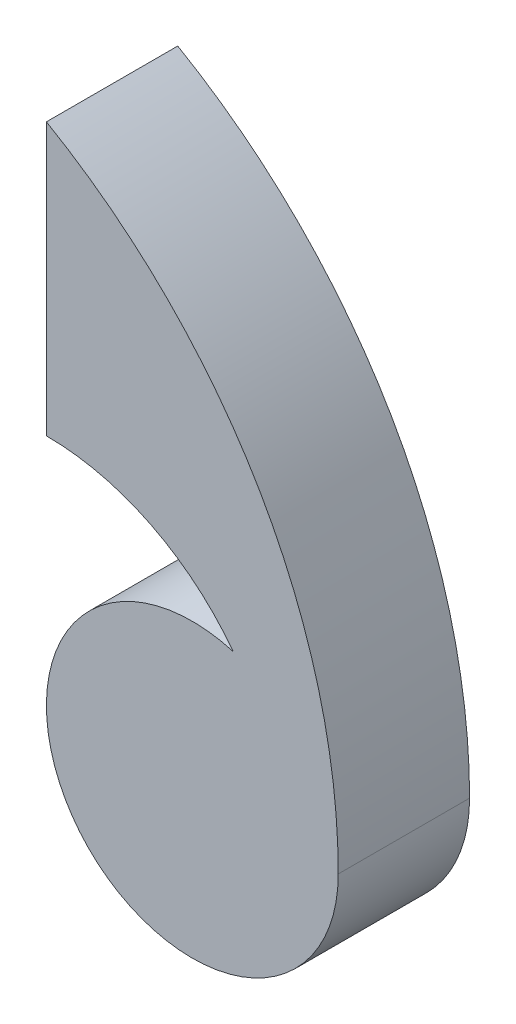
SolidWorks part; units mm, degrees
ref_plane "前视基准面" through (0, 0, 0) normal (0, 0, 1) x (1, 0, 0)
ref_plane "上视基准面" through (0, 0, 0) normal (0, 1, 0) x (1, 0, 0)
ref_plane "右视基准面" through (0, 0, 0) normal (1, 0, 0) x (0, 0, -1)
sketch "草图1" plane through (0, 0, 0) normal (0, 0, 1) x (1, 0, 0)
  circle A0 centre (0, 0) radius 20
  dimension "D1" = 40
extrude "凸台-拉伸1" add sketch "草图1" along normal blind 18
sketch "草图2" plane through (0, 0, 18) normal (0, 0, 1) x (1, 0, 0)
  line L0 (0, 0) -> (-60, 0) construction
  line L1 (-20, 0) -> (-20, 85.9055) construction
  line L2 (-20, 69.282) -> (-20, 32)
  line L3 (12, 0) -> (20, 0)
  circle A0 centre (0, 0) radius 20 construction
  arc A1 (20, 0) -> (-20, 69.282) centre (-60, 0) ccw
  circle A2 centre (-20, 0) radius 30 construction
  arc A3 (-20, 32) -> (12, 0) centre (-20, 0) cw
  dimension "D2" = 80
  dimension "D3" = 60
  dimension "D4" = 32
  dimension "D1" = 60
extrude "凸台-拉伸2" add sketch "草图2" against normal up to surface (18 mm away) up to face at (20, 0, 0)
